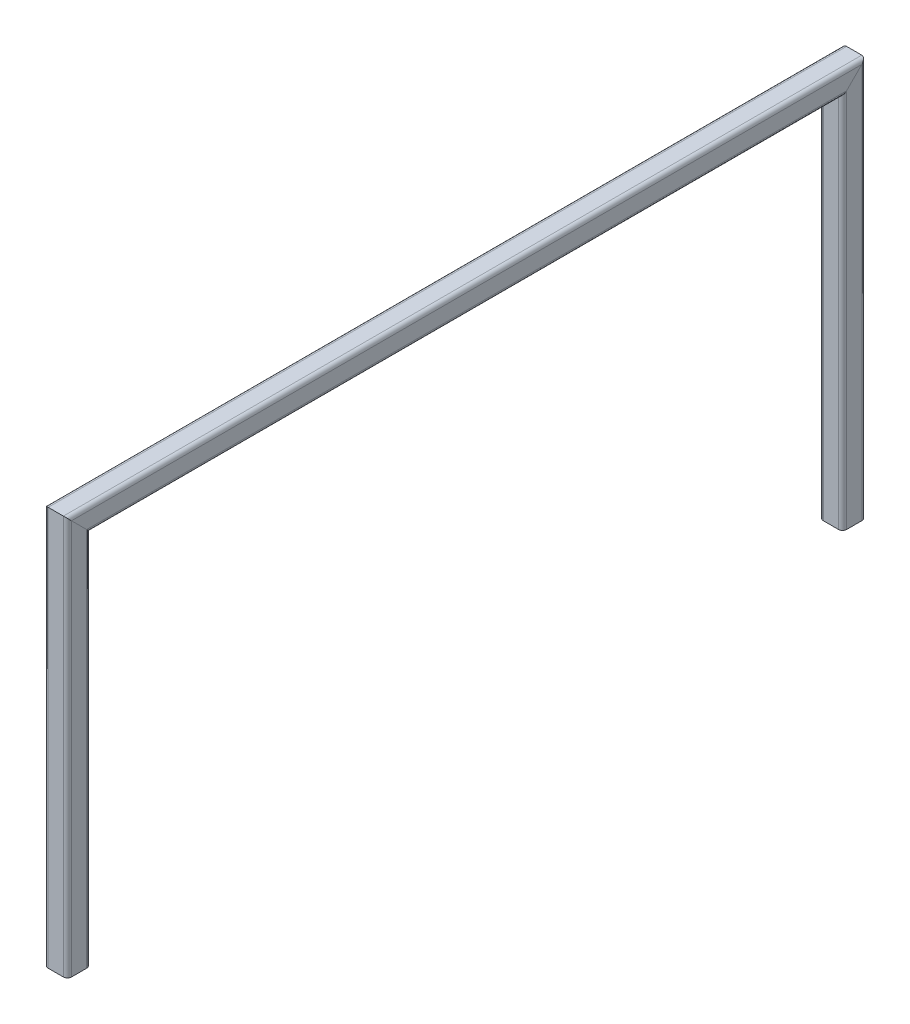
SolidWorks part; units mm, degrees
material "Alloy Steel"
ref_plane "Front Plane" through (0, 0, 0) normal (0, 0, 1) x (1, 0, 0)
ref_plane "Top Plane" through (0, 0, 0) normal (0, 1, 0) x (1, 0, 0)
ref_plane "Right Plane" through (0, 0, 0) normal (1, 0, 0) x (0, 0, -1)
sketch "Sketch1" plane through (0, 0, 0) normal (1, 0, 0) x (0, 0, -1)
  line L1 (500, 250) -> (-500, 250)
  line L2 (500, 250) -> (500, -250)
  line L3 (500, -250) -> (-500, -250)
  line L4 (-500, 250) -> (-500, -250)
  line L5 (500, 250) -> (-500, -250) construction
  line L6 (500, -250) -> (-500, 250) construction
  point P0 (0, 0)
  dimension "D1" = 1000
  dimension "D2" = 500
other "Square tube 30 X 30 X 2.6(1)"
ref_plane "Plane1" through (0, 250, -500) normal (0, -1, 0) x (0, 0, -1)
sketch "Sketch18" plane through (0, 250, -500) normal (0, -1, 0) x (0, 0, -1)
  line L0 (-9.8, -12.4) -> (9.8, -12.4)
  line L1 (-12.4, -9.8) -> (-12.4, 9.8)
  line L2 (9.8, 12.4) -> (-9.8, 12.4)
  line L3 (12.4, 9.8) -> (12.4, -9.8)
  line L4 (-9.8, -15) -> (9.8, -15)
  line L5 (-15, -9.8) -> (-15, 9.8)
  line L6 (9.8, 15) -> (-9.8, 15)
  line L7 (15, 9.8) -> (15, -9.8)
  arc A0 (15, 9.8) -> (9.8, 15) centre (9.8, 9.8) ccw
  arc A1 (9.8, -15) -> (15, -9.8) centre (9.8, -9.8) ccw
  arc A2 (-15, -9.8) -> (-9.8, -15) centre (-9.8, -9.8) ccw
  arc A3 (-9.8, 15) -> (-15, 9.8) centre (-9.8, 9.8) ccw
  arc A4 (-9.8, 12.4) -> (-12.4, 9.8) centre (-9.8, 9.8) ccw
  arc A5 (12.4, 9.8) -> (9.8, 12.4) centre (9.8, 9.8) ccw
  arc A6 (9.8, -12.4) -> (12.4, -9.8) centre (9.8, -9.8) ccw
  arc A7 (-12.4, -9.8) -> (-9.8, -12.4) centre (-9.8, -9.8) ccw
  point P0 (-15, 0)
  point P1 (15, 0)
  point P2 (0, 15)
  point P3 (0, -15)
  point P4 (0, 0)
  point P5 (-15, -15)
  point P6 (15, -15)
  point P7 (15, 15)
  point P8 (-15, 15)
  point P33 (0, 0)
  dimension "D1" = 5.2
  dimension "Thickness" = 2.6
  dimension "V_leg" = 30
ref_point "Point1"
sketch "Sketch19" plane through (0, 265, 0) normal (0, 1, 0) x (1, 0, 0)
  line L0 (0, 515) -> (0, -515) construction
  line L1 (9.8, 515) -> (-9.8, 515) construction
  line L2 (-9.8, -515) -> (9.8, -515) construction
  line L3 (-9.8, -315) -> (9.8, -315) construction
  line L4 (-9.8, 515) -> (-9.8, -515) construction
  line L5 (9.8, 515) -> (9.8, -515) construction
  line L6 (-9.8, 315) -> (9.8, 315) construction
  line L7 (-9.8, 515) -> (9.8, 515) construction
  point P16 (-9.8, -443.5381)
  dimension "D1" = 200
  dimension "D2" = 200
ref_point "Point3"
ref_point "Point4"
